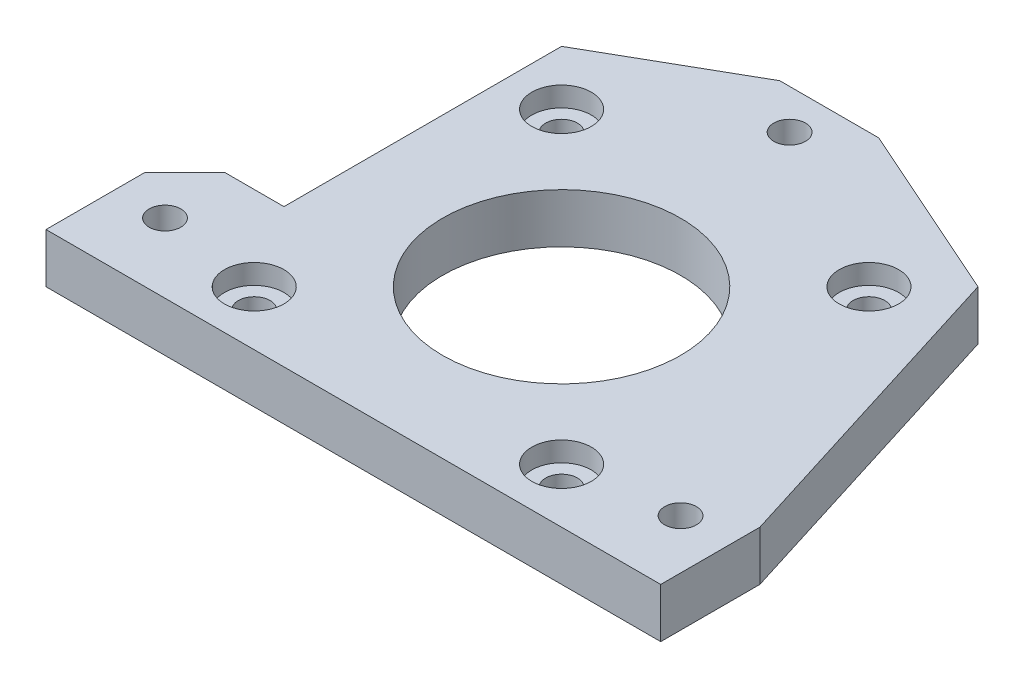
SolidWorks part; units mm, degrees
ref_plane "Front Plane" through (0, 0, 0) normal (0, 0, 1) x (1, 0, 0)
ref_plane "Top Plane" through (0, 0, 0) normal (0, 1, 0) x (1, 0, 0)
ref_plane "Right Plane" through (0, 0, 0) normal (1, 0, 0) x (0, 0, -1)
sketch "Sketch1" plane through (0, 0, 0) normal (0, 1, 0) x (1, 0, 0)
  line L7 (-15.5, 15.5) -> (15.5, 15.5) construction
  line L15 (-21, -21) -> (21, -21)
  line L18 (-21, -21) -> (-21, 21)
  line L19 (-21, 21) -> (21, 21)
  line L20 (21, -21) -> (21, 21)
  line L25 (-21, -21) -> (21, 21) construction
  line L26 (-21, 21) -> (21, -21) construction
  line L27 (15.5, 15.5) -> (15.5, -15.5) construction
  line L28 (15.5, -15.5) -> (-15.5, -15.5) construction
  line L29 (-15.5, -15.5) -> (-15.5, 15.5) construction
  line L30 (-27, -7) -> (-31, -11)
  line L31 (-21, -21) -> (-31, -21)
  line L32 (-21, -21) -> (-21, -7)
  line L33 (-21, -7) -> (-27, -7)
  line L34 (-31, -21) -> (-31, -11)
  line L35 (0, 0) -> (0, -21) construction
  line L36 (0, 0) -> (15.5, 0) construction
  line L37 (31, -21) -> (31, -11)
  line L38 (21, -7) -> (27, -7)
  line L39 (21, -21) -> (31, -21)
  line L40 (27, -7) -> (31, -11)
  line L41 (-11, 21) -> (-7, 29)
  line L42 (-7, 29) -> (3, 29)
  line L43 (3, 29) -> (7, 21)
  line L44 (-2, 29) -> (-2, 21) construction
  line L45 (31, -11) -> (21, 21)
  line L46 (-21, 21) -> (-7, 29)
  line L47 (3, 29) -> (21, 21)
  circle A2 centre (15.5, -15.5) radius 1.6
  circle A12 centre (-15.5, -15.5) radius 1.6
  circle A13 centre (-15.5, 15.5) radius 1.6
  circle A14 centre (15.5, 15.5) radius 1.6
  circle A15 centre (0, 0) radius 12
  circle A16 centre (-26, -14) radius 1.6
  circle A17 centre (-26, -14) radius 5 construction
  circle A18 centre (26, -14) radius 5 construction
  circle A19 centre (26, -14) radius 1.6
  circle A20 centre (-2, 25) radius 1.6
  circle A21 centre (-2, 25) radius 4 construction
  point P0 (0, 0)
  point P16 (-31, -7)
  point P28 (31, -7)
  dimension "D6" = 3.2
  dimension "D7" = 31
  dimension "D8" = 24
  dimension "D9" = 14
  dimension "D10" = 10
  dimension "D11" = 3.2
  dimension "D16" = 3.2
  dimension "D19" = 9
  dimension "D20" = 11
  dimension "D3" = 3.2
  dimension "D4" = 3.2
  dimension "D5" = 3.2
  dimension "D12" = 10
  dimension "D13" = 7
  dimension "D18" = 8
  dimension "D1" = 42
  dimension "D2" = 42
  dimension "D14" = 10
  dimension "D15" = 9
extrude "Boss-Extrude1" add sketch "Sketch1" along normal blind 5 contours L15 L20 L19 L18 A15 A14 A13 A12 A2 | L34 L31 L18 L33 L30 A16 | L40 L38 L20 L39 L37 A19 | L43 L42 L41 L19 A20 | L40 L45 L20 L38 | L46 L19 L41 | L47 L43 L19
sketch "Sketch2" plane through (0, 5, 0) normal (0, 1, 0) x (1, 0, 0)
  line L0 (-26, -14) -> (26, -14)
  line L1 (-2, -14) -> (-2, 25)
  line L2 (-31, -21) -> (31, -21) construction
  line L3 (0, 0) -> (0, -21)
  dimension "D1" = 52
  dimension "D2" = 39
  dimension "D3" = 7
  dimension "D4" = 24
  dimension "D5" = 21
  dimension "D6" = 26
sketch "Sketch3" plane through (0, 5, 0) normal (0, 1, 0) x (1, 0, 0)
  circle A0 centre (-15.5, 15.5) radius 3
  circle A1 centre (15.5, 15.5) radius 3
  circle A2 centre (15.5, -15.5) radius 3
  circle A3 centre (-15.5, -15.5) radius 3
  dimension "D1" = 6
  dimension "D2" = 6
  dimension "D3" = 6
  dimension "D4" = 6
extrude "Cut-Extrude1" cut sketch "Sketch3" against normal blind 2
